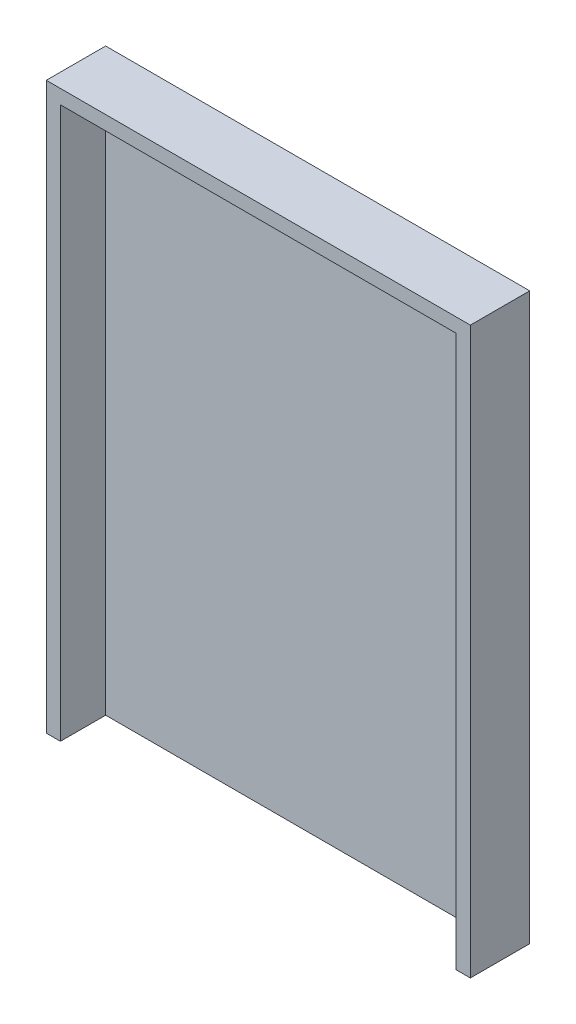
SolidWorks part; units mm, degrees
ref_plane "前视基准面" through (0, 0, 0) normal (0, 0, 1) x (1, 0, 0)
ref_plane "上视基准面" through (0, 0, 0) normal (0, 1, 0) x (1, 0, 0)
ref_plane "右视基准面" through (0, 0, 0) normal (1, 0, 0) x (0, 0, -1)
sketch "草图1" plane through (0, 0, 0) normal (0, 0, 1) x (1, 0, 0)
  line L0 (-34.953, 27.8881) -> (265.047, 27.8881)
  line L1 (265.047, 27.8881) -> (265.047, -372.1119)
  line L2 (265.047, -372.1119) -> (-34.953, -372.1119)
  line L3 (-34.953, -372.1119) -> (-34.953, 27.8881)
extrude "凸台-拉伸1" add sketch "草图1" along normal blind 10
sketch "草图2" plane through (0, 0, 10) normal (0, 0, 1) x (1, 0, 0)
  line L0 (265.047, -372.1119) -> (265.047, 27.8881)
  line L1 (265.047, 27.8881) -> (-34.953, 27.8881) construction
  line L2 (265.047, -372.1119) -> (265.047, 27.8881) construction
  line L3 (265.047, 27.8881) -> (-34.953, 27.8881)
  line L4 (-34.953, 27.8881) -> (-34.953, -372.1119)
  line L5 (-34.953, -372.1119) -> (-24.953, -372.1119)
  line L6 (-34.953, -372.1119) -> (265.047, -372.1119) construction
  line L7 (-24.953, -372.1119) -> (-24.953, 17.8881)
  line L8 (-24.953, 17.8881) -> (255.047, 17.8881)
  line L9 (255.047, 17.8881) -> (255.047, -372.1119)
  line L10 (255.047, -372.1119) -> (265.047, -372.1119)
extrude "凸台-拉伸2" add sketch "草图2" along normal blind 32
